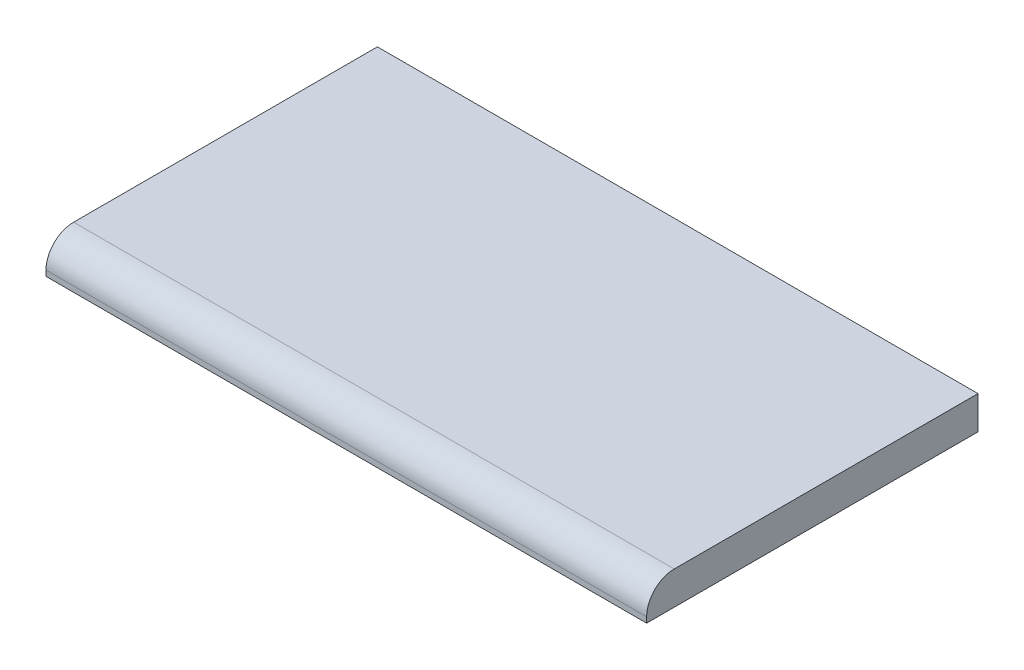
SolidWorks part; units mm, degrees
material "AISI 4130 Steel, normalized at 870C"
ref_plane "Front Plane" through (0, 0, 0) normal (0, 0, 1) x (1, 0, 0)
ref_plane "Top Plane" through (0, 0, 0) normal (0, 1, 0) x (1, 0, 0)
ref_plane "Right Plane" through (0, 0, 0) normal (1, 0, 0) x (0, 0, -1)
sketch "Sketch1" plane through (0, 0, 0) normal (0, 1, 0) x (1, 0, 0)
  line L0 (0, 149.352) -> (0, 150.876) construction
  line L1 (0, 0) -> (273.177, 0)
  line L2 (0, 0) -> (0, 149.352)
  line L3 (0, 149.352) -> (273.177, 149.352)
  line L4 (273.177, 0) -> (273.177, 149.352)
  line L5 (-1.524, -1.524) -> (274.701, -1.524)
  line L6 (-1.524, -1.524) -> (-1.524, 150.876)
  line L7 (-1.524, 150.876) -> (274.701, 150.876)
  line L8 (274.701, -1.524) -> (274.701, 150.876)
  line L9 (273.177, 149.352) -> (274.701, 149.352) construction
  line L10 (273.177, 0) -> (273.177, -1.524) construction
  line L11 (0, 0) -> (-1.524, 0) construction
  line L13 (0, 0) -> (273.177, 0)
  line L14 (0, 0) -> (0, 149.352)
  line L15 (0, 149.352) -> (273.177, 149.352)
  line L16 (273.177, 0) -> (273.177, 149.352)
  dimension "D1" = 1.524
  dimension "D2" = 276.225
  dimension "D3" = 152.4
extrude "Bulk-Extrude" add sketch "Sketch1" along normal blind 15.24 contours L1 L4 L3 L2 | L5 L8 L7 L6 L4 L1 L2 L3
fillet "Fillet1" radius 12.7 1 edges at (136.5885, 15.24, 1.524)
shell "Shell" thickness 1.524
ref_plane "Mid Plane" through (136.5885, 0, 0) normal (1, 0, 0) x (0, 0, -1)
sketch "Sketch2" plane through (136.5885, 0, 0) normal (1, 0, 0) x (0, 0, -1)
  line L0 (150.876, 0) -> (154.051, 0)
  line L1 (154.051, 3.175) -> (150.876, 3.175)
  line L2 (150.876, 15.24) -> (150.876, 0) construction
  line L3 (150.876, 3.175) -> (150.876, 0)
  circle A0 centre (154.051, 0) radius 3.175
  circle A1 centre (154.051, 0) radius 1.651
  dimension "D1" = 1.524
  dimension "D2" = 6.35
extrude "Boss-Extrude3" add sketch "Sketch2" along normal mid plane 101.6
